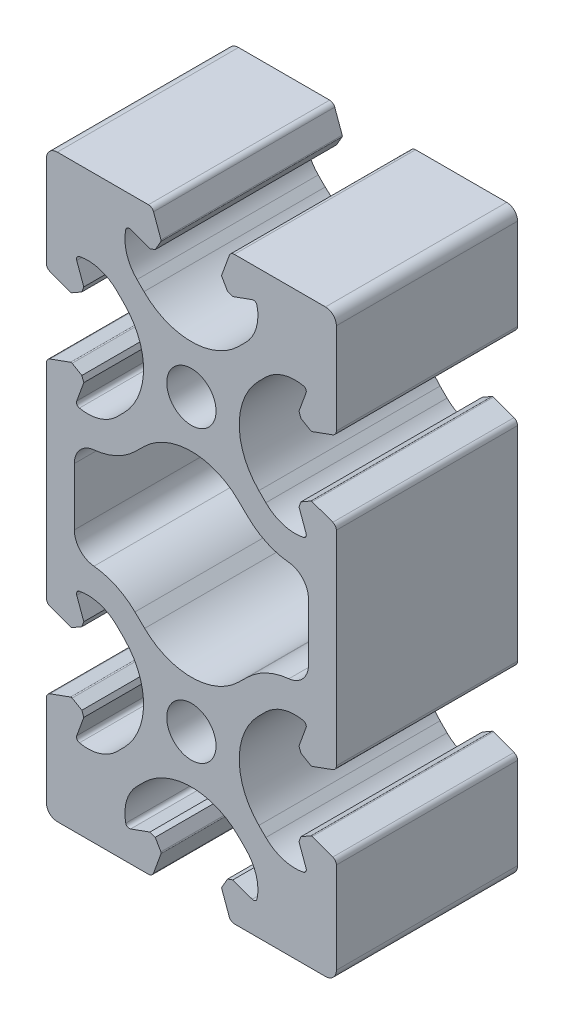
SolidWorks part; units mm, degrees
material "6005-T5"
ref_plane "Front" through (0, 0, 0) normal (0, 0, 1) x (1, 0, 0)
ref_plane "Top" through (0, 0, 0) normal (0, 1, 0) x (1, 0, 0)
ref_plane "Right" through (0, 0, 0) normal (1, 0, 0) x (0, 0, -1)
sketch "Sk Main Extrusion" plane through (0, 0, 0) normal (0, 0, 1) x (1, 0, 0)
  line L84 (-6.4502, 10.8801) -> (-7.7859, 9.5806)
  line L85 (-16.15, 3.9645) -> (-16.15, -3.9645)
  line L86 (-7.7859, -9.5806) -> (-6.4502, -10.8801)
  line L87 (6.4502, -10.8801) -> (7.7859, -9.5806)
  line L88 (16.15, -3.9645) -> (16.15, 3.9645)
  line L89 (7.7859, 9.5806) -> (6.4502, 10.8801)
  line L90 (16.6712, 24.1901) -> (19.5065, 25.2221)
  line L91 (20, 25.9268) -> (20, 38.5)
  line L92 (18.5, 40) -> (5.9268, 40)
  line L93 (5.2221, 39.5065) -> (4.1901, 36.6712)
  line L94 (4.2085, 36.4607) -> (4.9876, 35.1113)
  line L95 (4.9876, 35.1113) -> (5.7185, 34.8453)
  line L96 (5.7185, 34.8453) -> (8.3962, 35.8198)
  line L97 (7.5042, 30.2727) -> (6.5407, 29.3093)
  line L98 (-6.5407, 29.3093) -> (-7.5042, 30.2727)
  line L99 (-8.3962, 35.8198) -> (-5.7185, 34.8453)
  line L100 (-5.7185, 34.8453) -> (-4.9876, 35.1113)
  line L101 (-4.9876, 35.1113) -> (-4.2085, 36.4607)
  line L102 (-4.1901, 36.6712) -> (-5.2221, 39.5065)
  line L103 (-5.9268, 40) -> (-18.5, 40)
  line L104 (-20, 38.5) -> (-20, 25.9268)
  line L105 (-19.5065, 25.2221) -> (-16.6712, 24.1901)
  line L106 (-16.4607, 24.2085) -> (-15.1113, 24.9876)
  line L107 (-15.1113, 24.9876) -> (-14.8453, 25.7185)
  line L108 (-14.8453, 25.7185) -> (-15.8198, 28.3962)
  line L109 (-10.2727, 27.5042) -> (-9.3093, 26.5407)
  line L110 (-9.3093, 13.4593) -> (-10.2727, 12.4958)
  line L111 (-15.8198, 11.6038) -> (-14.8453, 14.2815)
  line L112 (-14.8453, 14.2815) -> (-15.1113, 15.0124)
  line L113 (-15.1113, 15.0124) -> (-16.4607, 15.7915)
  line L114 (-16.6712, 15.8099) -> (-19.5065, 14.7779)
  line L115 (-20, 14.0732) -> (-20, -14.0732)
  line L116 (-19.5065, -14.7779) -> (-16.6712, -15.8099)
  line L117 (-16.4607, -15.7915) -> (-15.1113, -15.0124)
  line L118 (-15.1113, -15.0124) -> (-14.8453, -14.2815)
  line L119 (-14.8453, -14.2815) -> (-15.8198, -11.6038)
  line L120 (-10.2727, -12.4958) -> (-9.3093, -13.4593)
  line L121 (-9.3093, -26.5407) -> (-10.2727, -27.5042)
  line L122 (-15.8198, -28.3962) -> (-14.8453, -25.7185)
  line L123 (-14.8453, -25.7185) -> (-15.1113, -24.9876)
  line L124 (-15.1113, -24.9876) -> (-16.4607, -24.2085)
  line L125 (-16.6712, -24.1901) -> (-19.5065, -25.2221)
  line L126 (-20, -25.9268) -> (-20, -38.5)
  line L127 (-18.5, -40) -> (-5.9268, -40)
  line L128 (-5.2221, -39.5065) -> (-4.1901, -36.6712)
  line L129 (-4.2085, -36.4607) -> (-4.9876, -35.1113)
  line L130 (-4.9876, -35.1113) -> (-5.7185, -34.8453)
  line L131 (-5.7185, -34.8453) -> (-8.3962, -35.8198)
  line L132 (-7.5042, -30.2727) -> (-6.5407, -29.3093)
  line L133 (6.5407, -29.3093) -> (7.5042, -30.2727)
  line L134 (8.3962, -35.8198) -> (5.7185, -34.8453)
  line L135 (5.7185, -34.8453) -> (4.9876, -35.1113)
  line L136 (4.9876, -35.1113) -> (4.2085, -36.4607)
  line L137 (4.1901, -36.6712) -> (5.2221, -39.5065)
  line L138 (5.9268, -40) -> (18.5, -40)
  line L139 (20, -38.5) -> (20, -25.9268)
  line L140 (19.5065, -25.2221) -> (16.6712, -24.1901)
  line L141 (16.4607, -24.2085) -> (15.1113, -24.9876)
  line L142 (15.1113, -24.9876) -> (14.8453, -25.7185)
  line L143 (14.8453, -25.7185) -> (15.8198, -28.3962)
  line L144 (10.2727, -27.5042) -> (9.3093, -26.5407)
  line L145 (9.3093, -13.4593) -> (10.2727, -12.4958)
  line L146 (15.8198, -11.6038) -> (14.8453, -14.2815)
  line L147 (14.8453, -14.2815) -> (15.1113, -15.0124)
  line L148 (15.1113, -15.0124) -> (16.4607, -15.7915)
  line L149 (16.6712, -15.8099) -> (19.5065, -14.7779)
  line L150 (20, -14.0732) -> (20, 14.0732)
  line L151 (19.5065, 14.7779) -> (16.6712, 15.8099)
  line L152 (16.4607, 15.7915) -> (15.1113, 15.0124)
  line L153 (15.1113, 15.0124) -> (14.8453, 14.2815)
  line L154 (14.8453, 14.2815) -> (15.8198, 11.6038)
  line L155 (10.2727, 12.4958) -> (9.3093, 13.4593)
  line L156 (9.3093, 26.5407) -> (10.2727, 27.5042)
  line L157 (15.8198, 28.3962) -> (14.8453, 25.7185)
  line L158 (14.8453, 25.7185) -> (15.1113, 24.9876)
  line L159 (15.1113, 24.9876) -> (16.4607, 24.2085)
  circle A70 centre (0, -20) radius 3.4
  circle A71 centre (0, 20) radius 3.4
  arc A72 (-13.4453, 6.9499) -> (-7.7859, 9.5806) centre (-14.3755, 16.354) ccw
  arc A73 (-13.4453, 6.9499) -> (-16.15, 3.9645) centre (-13.15, 3.9645) ccw
  arc A74 (-16.15, -3.9645) -> (-13.4453, -6.9499) centre (-13.15, -3.9645) ccw
  arc A75 (-7.7859, -9.5806) -> (-13.4453, -6.9499) centre (-14.3755, -16.354) ccw
  arc A76 (-6.4502, -10.8801) -> (6.4502, -10.8801) centre (0, -4.25) ccw
  arc A77 (13.4453, -6.9499) -> (7.7859, -9.5806) centre (14.3755, -16.354) ccw
  arc A78 (13.4453, -6.9499) -> (16.15, -3.9645) centre (13.15, -3.9645) ccw
  arc A79 (16.15, 3.9645) -> (13.4453, 6.9499) centre (13.15, 3.9645) ccw
  arc A80 (7.7859, 9.5806) -> (13.4453, 6.9499) centre (14.3755, 16.354) ccw
  arc A81 (6.4502, 10.8801) -> (-6.4502, 10.8801) centre (0, 4.25) ccw
  arc A82 (19.5065, 25.2221) -> (20, 25.9268) centre (19.25, 25.9268) ccw
  arc A83 (20, 38.5) -> (18.5, 40) centre (18.5, 38.5) ccw
  arc A84 (5.9268, 40) -> (5.2221, 39.5065) centre (5.9268, 39.25) ccw
  arc A85 (4.1901, 36.6712) -> (4.2085, 36.4607) centre (4.425, 36.5857) ccw
  arc A86 (9.057, 35.4507) -> (8.3962, 35.8198) centre (8.5672, 35.35) ccw
  arc A87 (7.5042, 30.2727) -> (9.057, 35.4507) centre (3.4737, 34.3032) ccw
  arc A88 (-6.5407, 29.3093) -> (6.5407, 29.3093) centre (0, 35.85) ccw
  arc A89 (-9.057, 35.4507) -> (-7.5042, 30.2727) centre (-3.4737, 34.3032) ccw
  arc A90 (-8.3962, 35.8198) -> (-9.057, 35.4507) centre (-8.5672, 35.35) ccw
  arc A91 (-4.2085, 36.4607) -> (-4.1901, 36.6712) centre (-4.425, 36.5857) ccw
  arc A92 (-5.2221, 39.5065) -> (-5.9268, 40) centre (-5.9268, 39.25) ccw
  arc A93 (-18.5, 40) -> (-20, 38.5) centre (-18.5, 38.5) ccw
  arc A94 (-20, 25.9268) -> (-19.5065, 25.2221) centre (-19.25, 25.9268) ccw
  arc A95 (-16.6712, 24.1901) -> (-16.4607, 24.2085) centre (-16.5857, 24.425) ccw
  arc A96 (-15.4507, 29.057) -> (-15.8198, 28.3962) centre (-15.35, 28.5672) ccw
  arc A97 (-10.2727, 27.5042) -> (-15.4507, 29.057) centre (-14.3032, 23.4737) ccw
  arc A98 (-9.3093, 13.4593) -> (-9.3093, 26.5407) centre (-15.85, 20) ccw
  arc A99 (-15.4507, 10.943) -> (-10.2727, 12.4958) centre (-14.3032, 16.5263) ccw
  arc A100 (-15.8198, 11.6038) -> (-15.4507, 10.943) centre (-15.35, 11.4328) ccw
  arc A101 (-16.4607, 15.7915) -> (-16.6712, 15.8099) centre (-16.5857, 15.575) ccw
  arc A102 (-19.5065, 14.7779) -> (-20, 14.0732) centre (-19.25, 14.0732) ccw
  arc A103 (-20, -14.0732) -> (-19.5065, -14.7779) centre (-19.25, -14.0732) ccw
  arc A104 (-16.6712, -15.8099) -> (-16.4607, -15.7915) centre (-16.5857, -15.575) ccw
  arc A105 (-15.4507, -10.943) -> (-15.8198, -11.6038) centre (-15.35, -11.4328) ccw
  arc A106 (-10.2727, -12.4958) -> (-15.4507, -10.943) centre (-14.3032, -16.5263) ccw
  arc A107 (-9.3093, -26.5407) -> (-9.3093, -13.4593) centre (-15.85, -20) ccw
  arc A108 (-15.4507, -29.057) -> (-10.2727, -27.5042) centre (-14.3032, -23.4737) ccw
  arc A109 (-15.8198, -28.3962) -> (-15.4507, -29.057) centre (-15.35, -28.5672) ccw
  arc A110 (-16.4607, -24.2085) -> (-16.6712, -24.1901) centre (-16.5857, -24.425) ccw
  arc A111 (-19.5065, -25.2221) -> (-20, -25.9268) centre (-19.25, -25.9268) ccw
  arc A112 (-20, -38.5) -> (-18.5, -40) centre (-18.5, -38.5) ccw
  arc A113 (-5.9268, -40) -> (-5.2221, -39.5065) centre (-5.9268, -39.25) ccw
  arc A114 (-4.1901, -36.6712) -> (-4.2085, -36.4607) centre (-4.425, -36.5857) ccw
  arc A115 (-9.057, -35.4507) -> (-8.3962, -35.8198) centre (-8.5672, -35.35) ccw
  arc A116 (-7.5042, -30.2727) -> (-9.057, -35.4507) centre (-3.4737, -34.3032) ccw
  arc A117 (6.5407, -29.3093) -> (-6.5407, -29.3093) centre (0, -35.85) ccw
  arc A118 (9.057, -35.4507) -> (7.5042, -30.2727) centre (3.4737, -34.3032) ccw
  arc A119 (8.3962, -35.8198) -> (9.057, -35.4507) centre (8.5672, -35.35) ccw
  arc A120 (4.2085, -36.4607) -> (4.1901, -36.6712) centre (4.425, -36.5857) ccw
  arc A121 (5.2221, -39.5065) -> (5.9268, -40) centre (5.9268, -39.25) ccw
  arc A122 (18.5, -40) -> (20, -38.5) centre (18.5, -38.5) ccw
  arc A123 (20, -25.9268) -> (19.5065, -25.2221) centre (19.25, -25.9268) ccw
  arc A124 (16.6712, -24.1901) -> (16.4607, -24.2085) centre (16.5857, -24.425) ccw
  arc A125 (15.4507, -29.057) -> (15.8198, -28.3962) centre (15.35, -28.5672) ccw
  arc A126 (10.2727, -27.5042) -> (15.4507, -29.057) centre (14.3032, -23.4737) ccw
  arc A127 (9.3093, -13.4593) -> (9.3093, -26.5407) centre (15.85, -20) ccw
  arc A128 (15.4507, -10.943) -> (10.2727, -12.4958) centre (14.3032, -16.5263) ccw
  arc A129 (15.8198, -11.6038) -> (15.4507, -10.943) centre (15.35, -11.4328) ccw
  arc A130 (16.4607, -15.7915) -> (16.6712, -15.8099) centre (16.5857, -15.575) ccw
  arc A131 (19.5065, -14.7779) -> (20, -14.0732) centre (19.25, -14.0732) ccw
  arc A132 (20, 14.0732) -> (19.5065, 14.7779) centre (19.25, 14.0732) ccw
  arc A133 (16.6712, 15.8099) -> (16.4607, 15.7915) centre (16.5857, 15.575) ccw
  arc A134 (15.4507, 10.943) -> (15.8198, 11.6038) centre (15.35, 11.4328) ccw
  arc A135 (10.2727, 12.4958) -> (15.4507, 10.943) centre (14.3032, 16.5263) ccw
  arc A136 (9.3093, 26.5407) -> (9.3093, 13.4593) centre (15.85, 20) ccw
  arc A137 (15.4507, 29.057) -> (10.2727, 27.5042) centre (14.3032, 23.4737) ccw
  arc A138 (15.8198, 28.3962) -> (15.4507, 29.057) centre (15.35, 28.5672) ccw
  arc A139 (16.4607, 24.2085) -> (16.6712, 24.1901) centre (16.5857, 24.425) ccw
  point P54 (0, 0)
extrude "Main Extrusion" add sketch "Sk Main Extrusion" against normal blind 25
sketch "Threaded Insert Mate Sketch" plane through (0, 0, 0) normal (0, 0, 1) x (1, 0, 0)
  line L0 (-16.15, 0) -> (16.15, 0) construction
  line L3 (16.15, -3.9645) -> (16.15, 3.9645) construction
  line L4 (-16.15, 3.9645) -> (-16.15, -3.9645) construction
  circle A0 centre (0, 32.7) radius 5.6515
  circle A2 centre (12.7, 20) radius 5.6515
  circle A4 centre (-12.7, 20) radius 5.6515
  circle A5 centre (-12.7, -20) radius 5.6515
  circle A7 centre (12.7, -20) radius 5.6515
  circle A8 centre (0, -32.7) radius 5.6515
  circle A9 centre (0, 7.3) radius 5.6515
  circle A10 centre (0, 20) radius 3.4 construction
  point P14 (0, 20)
  point P26 (0, -20)
  dimension "D2" = 11.303
  dimension "D1" = 12.7
  dimension "D3" = 4
equation "\"Weight kg\"= round ( \"SW-Mass\" , 2 )"
equation "\"Weight lbs\"= round ( \"SW-Mass\" * 2.2046 , 2 )"
equation "\"Length mm\"= round ( \"Length@Main Extrusion\" , 2 )"
equation "\"Length in\"= round ( \"Length@Main Extrusion\" / 25.4 , 3 )"
